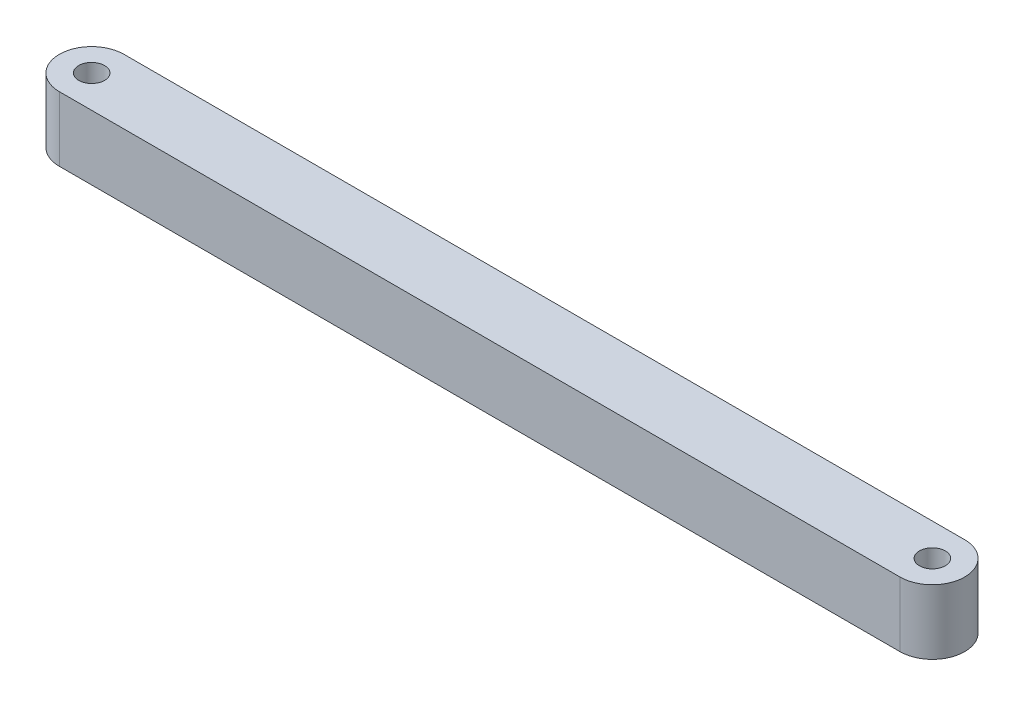
SolidWorks part; units mm, degrees
ref_plane "Front Plane" through (0, 0, 0) normal (0, 0, 1) x (1, 0, 0)
ref_plane "Top Plane" through (0, 0, 0) normal (0, 1, 0) x (1, 0, 0)
ref_plane "Right Plane" through (0, 0, 0) normal (1, 0, 0) x (0, 0, -1)
sketch "Sketch1" plane through (0, 0, 0) normal (0, 1, 0) x (1, 0, 0)
  line L0 (0, 0) -> (-65, 0) construction
  line L1 (0, -2.5) -> (-65, -2.5)
  line L2 (0, 2.5) -> (-65, 2.5)
  arc A0 (0, -2.5) -> (0, 2.5) centre (0, 0) ccw
  arc A1 (-65, 2.5) -> (-65, -2.5) centre (-65, 0) ccw
  point P3 (-32.5, 0)
  dimension "D2" = 2.5
  dimension "D1" = 65
extrude "Boss-Extrude1" add sketch "Sketch1" along normal blind 5
sketch "Sketch2" plane through (0, 5, 0) normal (0, 1, 0) x (1, 0, 0)
  circle A0 centre (-65, 0) radius 1
  circle A1 centre (0, 0) radius 1
  dimension "D1" = 2
  dimension "D2" = 2
extrude "Cut-Extrude1" cut sketch "Sketch2" against normal up to next
